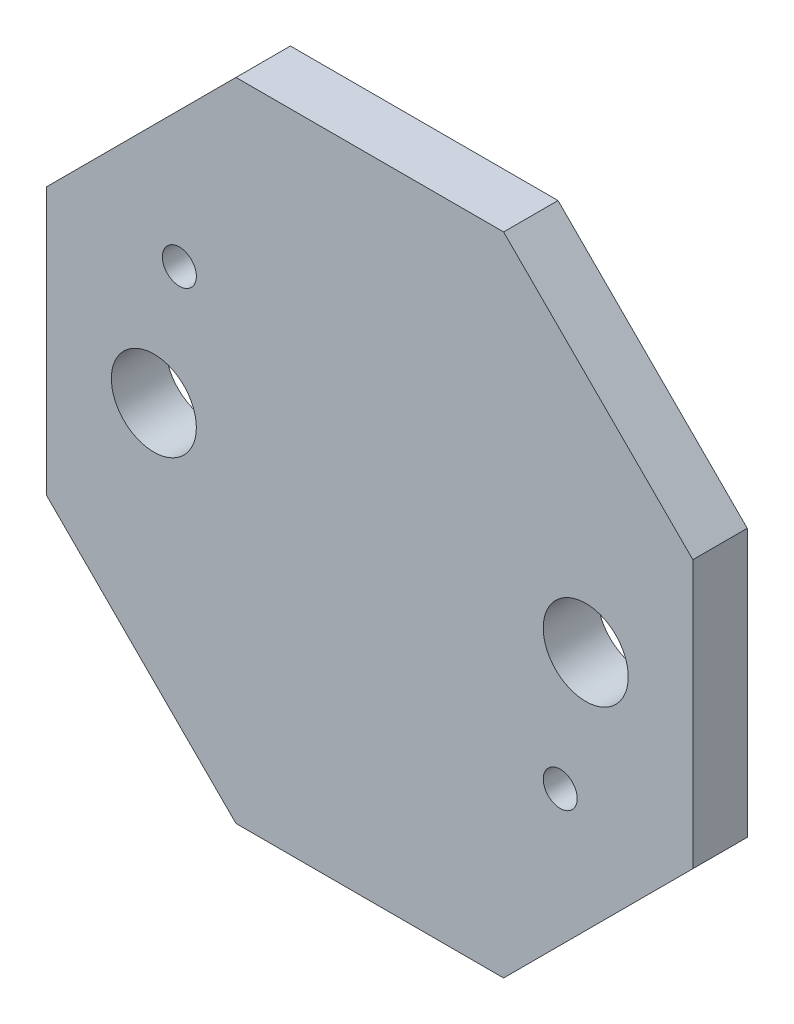
SolidWorks part; units mm, degrees
ref_plane "Front Plane" through (0, 0, 0) normal (0, 0, 1) x (1, 0, 0)
ref_plane "Top Plane" through (0, 0, 0) normal (0, 1, 0) x (1, 0, 0)
ref_plane "Right Plane" through (0, 0, 0) normal (1, 0, 0) x (0, 0, -1)
sketch "Sketch1" plane through (0, 0, 0) normal (0, 0, 1) x (1, 0, 0)
  line L0 (0, 0) -> (9.5, 0) construction
  line L9 (9.5, 3.935) -> (3.935, 9.5)
  line L10 (3.935, 9.5) -> (-3.935, 9.5)
  line L11 (-3.935, 9.5) -> (-9.5, 3.935)
  line L12 (-9.5, 3.935) -> (-9.5, -3.935)
  line L13 (-9.5, -3.935) -> (-3.935, -9.5)
  line L14 (-3.935, -9.5) -> (3.935, -9.5)
  line L15 (3.935, -9.5) -> (9.5, -3.935)
  line L16 (9.5, -3.935) -> (9.5, 3.935)
  line L17 (5.1, 0) -> (5.1, -3.85) construction
  circle A0 centre (0, 0) radius 10.2827 construction
  circle A1 centre (6.35, 0) radius 1.25
  circle A2 centre (5.6, -3.85) radius 0.5
  circle A3 centre (-6.35, 0) radius 1.25
  circle A4 centre (-5.6, 3.85) radius 0.5
  point P19 (0, 0)
  dimension "D1" = 9.5
  dimension "D2" = 2.5
  dimension "D3" = 3.15
  dimension "D4" = 1
  dimension "D5" = 3.85
  dimension "D6" = 2
extrude "Boss-Extrude1" add sketch "Sketch1" along normal blind 1.6
